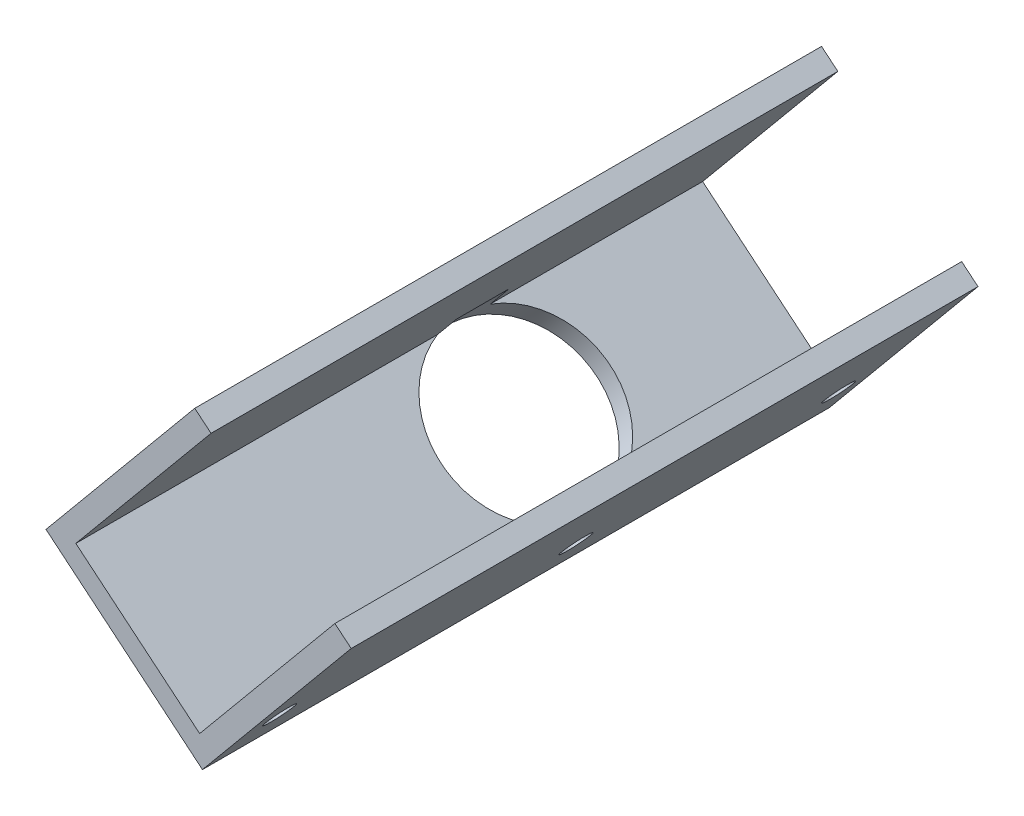
SolidWorks part; units mm, degrees
ref_plane "Piano frontale" through (0, 0, 0) normal (0, 0, 1) x (1, 0, 0)
ref_plane "Piano superiore" through (0, 0, 0) normal (0, 1, 0) x (1, 0, 0)
ref_plane "Piano destro" through (0, 0, 0) normal (1, 0, 0) x (0, 0, -1)
sketch "Schizzo1" plane through (0, 0, 0) normal (0, 0, 1) x (1, 0, 0)
  line L0 (1.3418, 31.372) -> (-14.622, 12.1325)
  line L1 (-14.622, 12.1325) -> (0, 0)
  line L2 (0, 0) -> (76.6263, 92.3494)
  line L3 (153.8056, 63.9969) -> (132.6371, 81.5614)
  line L4 (153.8056, 63.9969) -> (135.5951, 79.107) construction
  line L7 (125.0169, 92.3494) -> (132.6371, 81.5614)
  line L11 (125.8463, 92.9083) -> (135.5951, 79.107) construction
  line L12 (125.0169, 92.3494) -> (134.8547, 78.4219) construction
  line L13 (153.1671, 63.2273) -> (134.8547, 78.4219) construction
  line L14 (-0.131, 1.4081) -> (75.8181, 92.9413) construction
  line L15 (-13.2138, 12.2635) -> (-0.131, 1.4081) construction
  line L16 (2.1114, 30.7334) -> (-13.2138, 12.2635) construction
  arc A1 (125.0169, 92.3494) -> (76.6263, 92.3494) centre (100.8216, 76.8183) ccw
  arc A3 (125.8463, 92.9083) -> (75.8181, 92.9413) centre (100.8216, 76.8183) ccw construction
  dimension "D1" = 19
  dimension "D2" = 25
  dimension "D3" = 1
  dimension "85" = 120
extrude "Estrusione-Sottile1" add sketch "Schizzo1" along normal blind 37 and the other way blind 37 thin
sketch "Schizzo2" plane through (1.9239, -1.5964, 0) normal (0.7696, -0.6386, 0) x (0, 0, -1)
  circle A6 centre (-6.5524, 114.8694) radius 1.7
  circle A7 centre (-6.5524, 104.0526) radius 1.7
  circle A8 centre (1.4523, 109.7105) radius 1.7
  circle A9 centre (9.457, 104.5515) radius 1.7
  circle A10 centre (1.5534, 98.8285) radius 1.7
  circle A11 centre (9.6592, 93.6044) radius 1.7
extrude "Taglio-Estrusione2" cut sketch "Schizzo2" against normal blind 23
sketch "Schizzo3" plane through (-1.5964, -1.9239, 0) normal (-0.6386, -0.7696, 0) x (0.7696, -0.6386, 0)
  line L0 (-21.5, -37) -> (-21.5, 37) construction
  circle A0 centre (-9.5, -8.8116) radius 10
  dimension "D1" = 20
  dimension "D2" = 12
extrude "Taglio-Estrusione3" cut sketch "Schizzo3" against normal blind 6
sketch "Schizzo4" plane through (0, 0, 0) normal (-0.7696, 0.6386, 0) x (0, 0, 1)
  line L0 (-37, 0) -> (-11.9341, 0) construction
  line L1 (-17, 40) -> (2, 40)
  line L2 (-17, 40) -> (-17, 75)
  line L3 (-17, 75) -> (2, 75)
  line L4 (2, 40) -> (2, 75)
  line L6 (-37, 0) -> (-37, 120) construction
  line L7 (37, 0) -> (37, 120) construction
  dimension "D1" = 40
  dimension "D2" = 75
  dimension "D3" = 20
  dimension "D4" = 35
extrude "Taglio-Estrusione4" cut sketch "Schizzo4" against normal blind 9
sketch "Schizzo5" plane through (0, 0, 0) normal (-0.7696, 0.6386, 0) x (0, 0, 1)
  circle A0 centre (33, 5.5) radius 1.7
  circle A1 centre (-33, 5.5) radius 1.7
  circle A2 centre (-2, 5.5) radius 1.7
extrude "Taglio-Estrusione5" cut sketch "Schizzo5" against normal blind 9
sketch "Schizzo6" plane through (0, 0, 0) normal (0, 0, 1) x (1, 0, 0)
  line L0 (1.3418, 31.372) -> (32.9912, 5.1111)
  line L1 (32.9912, 5.1111) -> (167.3459, 57.4151)
  line L2 (167.3459, 57.4151) -> (141.9554, 113.1881)
  line L3 (141.9554, 113.1881) -> (32.9846, 110.8256)
  line L4 (32.9846, 110.8256) -> (1.3418, 31.372)
  line L5 (-0.5821, 32.9683) -> (1.3418, 31.372) construction
extrude "Taglio-Estrusione6" cut sketch "Schizzo6" against normal through all both and the other way through all
